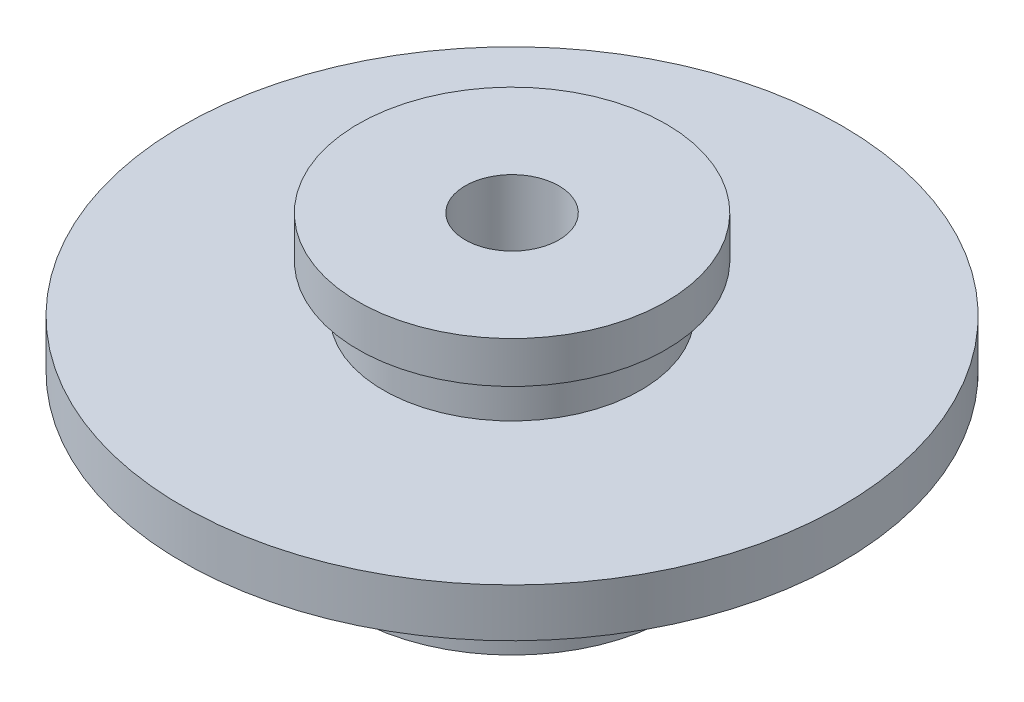
SolidWorks part; units mm, degrees
ref_plane "Спереди" through (0, 0, 0) normal (0, 0, 1) x (1, 0, 0)
ref_plane "Сверху" through (0, 0, 0) normal (0, 1, 0) x (1, 0, 0)
ref_plane "Справа" through (0, 0, 0) normal (1, 0, 0) x (0, 0, -1)
sketch "Эскиз1" plane through (0, 0, 0) normal (0, 0, 1) x (1, 0, 0)
  line L0 (2.9296, 0) -> (2.9296, 19.8706)
  line L1 (2.9296, 19.8706) -> (9.6248, 19.8706)
  line L2 (9.6248, 19.8706) -> (9.6248, 17.2772)
  line L3 (9.6248, 17.2772) -> (8.0482, 17.2772)
  line L4 (8.0482, 17.2772) -> (8.0482, 14.2942)
  line L5 (8.0482, 14.2942) -> (20.6007, 14.2942)
  line L6 (20.6007, 14.2942) -> (20.6007, 11.2727)
  line L7 (20.6007, 11.2727) -> (10, 11.2727)
  line L8 (10, 11.2727) -> (10, 3)
  line L10 (5, 0) -> (2.9296, 0)
  line L11 (0, -11.4414) -> (0, 79.8018) construction
  line L12 (5, 0) -> (5, 2)
  line L13 (5, 2) -> (10, 3)
  point P14 (2.9296, 0)
  point P15 (6.009, 0)
  point P17 (5.5647, 0)
  point P18 (0, 0)
  point P19 (0, 0)
  point P20 (0, 0)
revolve "Повернуть1" add sketch "Эскиз1" angle 360 about L11
